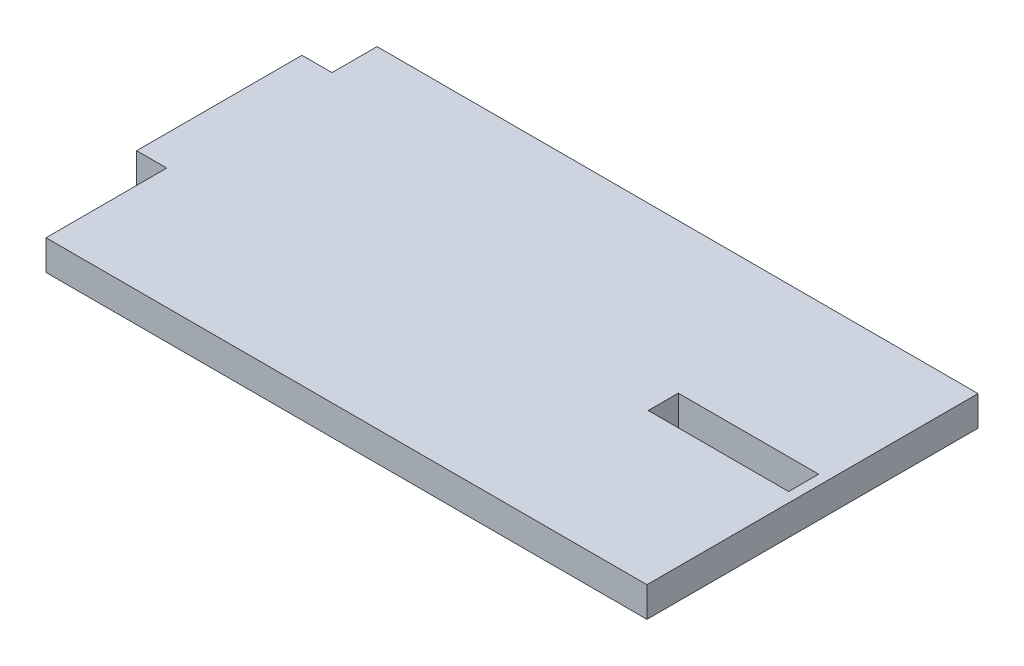
SolidWorks part; units mm, degrees
ref_plane "Front Plane" through (0, 0, 0) normal (0, 0, 1) x (1, 0, 0)
ref_plane "Top Plane" through (0, 0, 0) normal (0, 1, 0) x (1, 0, 0)
ref_plane "Right Plane" through (0, 0, 0) normal (1, 0, 0) x (0, 0, -1)
sketch "Sketch2" plane through (0, 0, 0) normal (0, 1, 0) x (1, 0, 0)
  line L0 (0, -6) -> (-4, -6)
  line L1 (0, 0) -> (80, 0)
  line L2 (0, 0) -> (0, -6)
  line L3 (0, -44.07) -> (80, -44.07)
  line L5 (-4, -6) -> (-4, -28)
  line L6 (-4, -28) -> (0, -28)
  line L7 (80, 0) -> (80, -36.6386) construction
  line L11 (0, -28) -> (0, -44.07)
  line L13 (8.7933, 0) -> (8.7933, -44.07) construction
  line L14 (60, -19.9) -> (78.689, -19.9)
  line L19 (80, 0) -> (80, -44.07)
  line L21 (60, -23.9) -> (78.689, -23.9)
  line L22 (78.689, -19.9) -> (78.689, -23.9)
  line L23 (60, -19.9) -> (60, -23.9)
  point P24 (80, -24.17)
  point P25 (100, -22.17)
  point P26 (60, -22.17)
  dimension "D1" = 80
  dimension "D2" = 44.07
  dimension "D3" = 4
  dimension "D4" = 22
  dimension "D5" = 6
  dimension "D6" = 19.9
extrude "Boss-Extrude1" add sketch "Sketch2" along normal blind 4
